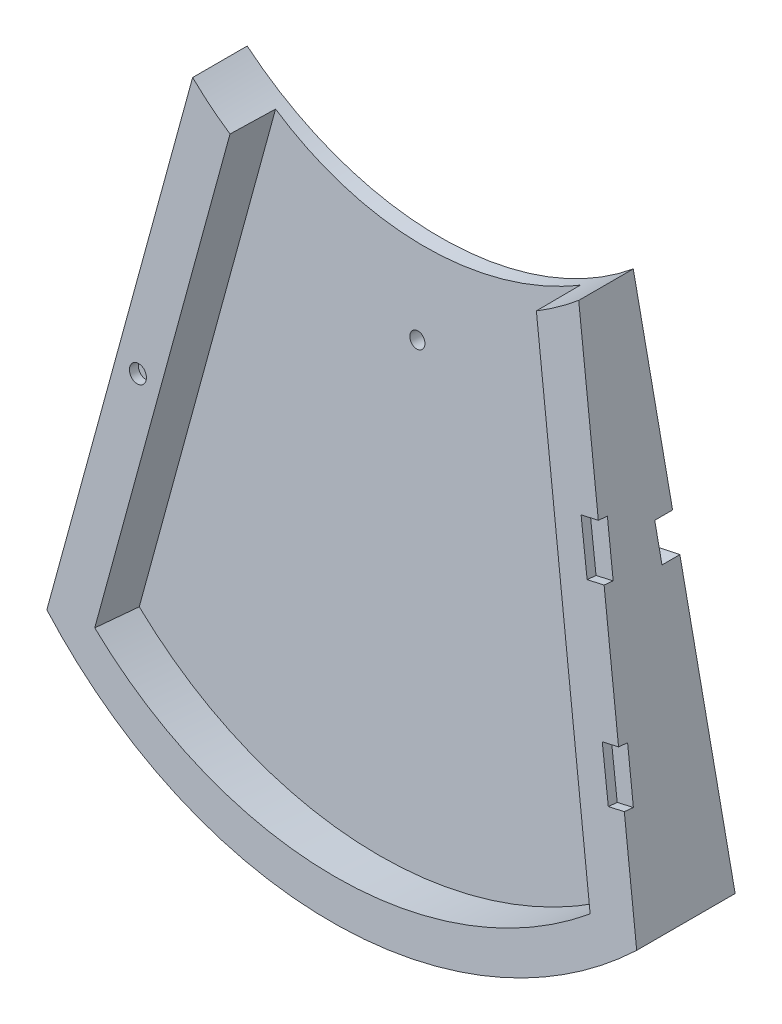
SolidWorks part; units mm, degrees
material "Oak"
ref_plane "Front Plane" through (0, 0, 0) normal (0, 0, 1) x (1, 0, 0)
ref_plane "Top Plane" through (0, 0, 0) normal (0, 1, 0) x (1, 0, 0)
ref_plane "Right Plane" through (0, 0, 0) normal (1, 0, 0) x (0, 0, -1)
sketch "Sketch2" plane through (0, 0, 0) normal (1, 0, 0) x (0, 0, -1)
  line L0 (-19.05, 177.8) -> (-34.9178, 0.7095)
  line L1 (-19.05, 177.8) -> (0, 177.8)
  line L4 (0, 177.8) -> (0, 0)
  line L5 (-34.9178, 0.7095) -> (-40.0182, -56.2125)
  line L6 (-40.0182, -56.2125) -> (0, -53.7905)
  line L7 (0, -53.7905) -> (0, 0)
  dimension "D1" = 19.05
  dimension "D2" = 34.925
  dimension "D3" = 177.8
  dimension "D4" = 57.15
extrude "Boss-Extrude1" add sketch "Sketch2" along normal blind 209.55
sketch "Sketch1" plane through (0, 0, 0) normal (0, 0, 1) x (1, 0, 0)
  line L0 (0, 0) -> (36.195, 174.0769)
  line L1 (173.355, 174.0769) -> (209.55, 0)
  line L2 (0, 0) -> (209.55, 0) construction
  line L3 (104.775, 149.4935) -> (104.775, -41.8231) construction
  line L4 (209.55, 177.8) -> (209.55, -56.2125) construction
  line L5 (-12.8433, 191.6723) -> (227.6672, 191.6723)
  line L6 (-12.8433, 191.6723) -> (-12.8433, -74.1551)
  line L7 (-12.8433, -74.1551) -> (227.6672, -74.1551)
  line L8 (227.6672, 191.6723) -> (227.6672, -74.1551)
  arc A2 (0, 0) -> (209.55, 0) centre (104.775, 110.6705) ccw
  arc A3 (36.195, 174.0769) -> (173.355, 174.0769) centre (104.775, 257.4435) ccw
  dimension "D1" = 107.95
  dimension "D3" = 152.4
  dimension "D2" = 177.8
  dimension "D4" = 137.16
  dimension "D5" = 215.9
extrude "Cut-Extrude1" cut sketch "Sketch1" along normal through all both and the other way through all
ref_plane "Plane1" through (0, -5.3911, -60.1672) normal (0, 0.0892, 0.996) x (1, 0, 0)
sketch "Sketch3" plane through (0, 3.4748, 34.67) normal (0, 0.0892, 0.996) x (1, 0, 0)
  line L0 (92.0294, 362.6105) -> (16.7736, -0.7763)
  line L1 (192.7764, -0.7763) -> (117.5206, 362.6105)
  line L2 (117.5206, 362.6105) -> (92.0294, 362.6105)
  line L3 (36.195, 171.2856) -> (0, -3.4887) construction
  line L4 (209.55, -3.4887) -> (173.355, 171.2856) construction
  arc A1 (16.7736, -0.7763) -> (192.7764, -0.7763) centre (104.775, 107.6252) ccw
  ellipse E0 centre (104.775, 107.6252) end of major axis (104.775, 260.6357) minor radius 152.4 (0, -3.4887) -> (209.55, -3.4887) ccw construction
  ellipse E1 centre (104.775, 254.9862) end of major axis (104.775, 363.3686) minor radius 107.95 (36.195, 171.2856) -> (173.355, 171.2856) ccw construction
  dimension "D2" = 15.875
extrude "Cut-Extrude2" cut sketch "Sketch3" against normal blind 15.875 contours L0 A1 L1 L2
sketch "Sketch4" plane through (0, 3.1095, 34.7027) normal (0, 0.0892, 0.996) x (1, 0, 0)
  line L0 (185.9702, 112.6051) -> (179.5857, 111.2457)
  line L2 (179.5857, 111.2457) -> (183.2886, 93.8555)
  line L3 (183.2886, 93.8555) -> (189.6731, 95.215)
  line L4 (189.6731, 95.215) -> (185.9702, 112.6051)
  line L5 (198.7566, 51.7026) -> (192.5459, 50.3802)
  line L6 (192.5459, 50.3802) -> (196.2488, 32.99)
  line L7 (196.2488, 32.99) -> (202.4595, 34.3125)
  line L8 (202.4595, 34.3125) -> (198.7566, 51.7026)
  line L9 (173.355, 173.3823) -> (209.55, 0) construction
  dimension "D1" = 17.78
  dimension "D2" = 38.1
  dimension "D3" = 44.45
  dimension "D4" = 6.35
extrude "Cut-Extrude3" cut sketch "Sketch4" against normal blind 3.175
sketch "Sketch5" plane through (0, 3.1095, 34.7027) normal (0, 0.0892, 0.996) x (1, 0, 0)
  line L0 (43.2755, 166.701) -> (6.8386, -9.2415) construction
  line L1 (36.195, 171.6524) -> (50.3561, 161.7497) construction
  line L2 (36.195, 171.6524) -> (0, -3.1219) construction
  circle A0 centre (25.0571, 78.7298) radius 3
  ellipse E1 centre (104.775, 107.992) end of major axis (104.775, 261.0025) minor radius 152.4 (0, -3.1219) -> (209.55, -3.1219) ccw construction
  dimension "D1" = 6
extrude "Cut-Extrude4" cut sketch "Sketch5" against normal blind 3.175
sketch "Sketch6" plane through (0, 0, 0) normal (0, 0, -1) x (-1, 0, 0)
  line L0 (-203.2, -5.6836) -> (-203.2, 0.6664)
  line L1 (-6.35, 0.6664) -> (-6.35, -5.6836)
  arc A1 (-203.2, 0.6664) -> (-6.35, 0.6664) centre (-104.775, 110.6705) ccw
  arc A2 (-203.2, -5.6836) -> (-6.35, -5.6836) centre (-104.775, 48.2914) ccw
  arc A3 (-209.55, 0) -> (0, 0) centre (-104.775, 110.6705) ccw construction
  dimension "D1" = 6.35
  dimension "D2" = 6.35
extrude "Cut-Extrude7" cut sketch "Sketch6" against normal blind 6.35 and the other way blind 3.175 contours A1 L1 A2 L0
sketch "Sketch7" plane through (0, 1.6927, 18.8911) normal (0, 0.0892, 0.996) x (1, 0, 0)
  circle A0 centre (104.775, 120.767) radius 2.667
  arc A2 (16.7736, -0.4095) -> (192.7764, -0.4095) centre (104.775, 107.992) ccw construction
  point P7 (104.775, -31.633)
  dimension "D1" = 5.334
  dimension "D2" = 152.4
extrude "Cut-Extrude8" cut sketch "Sketch7" against normal through all contours A0
sketch "Sketch8" plane through (0, 0, 0) normal (0, 0, -1) x (-1, 0, 0)
  line L0 (-187.325, 106.8893) -> (-189.9104, 94.4553)
  line L1 (-209.55, 0) -> (-173.355, 174.0769) construction
  line L2 (-189.9104, 94.4553) -> (-179.3414, 92.2577)
  line L3 (-179.3414, 92.2577) -> (-176.756, 104.6918)
  line L4 (-176.756, 104.6918) -> (-187.325, 106.8893)
  line L5 (-104.775, 121.9778) -> (-104.775, -41.7295) construction
  line L6 (-32.794, 104.6918) -> (-22.225, 106.8893)
  line L7 (-30.2086, 92.2577) -> (-32.794, 104.6918)
  line L8 (-19.6396, 94.4553) -> (-30.2086, 92.2577)
  line L9 (-22.225, 106.8893) -> (-19.6396, 94.4553)
  arc A0 (-203.2, -5.6836) -> (-6.35, -5.6836) centre (-104.775, 110.6705) ccw construction
  dimension "D1" = 12.7
  dimension "D2" = 10.795
  dimension "D3" = 82.55
extrude "Cut-Extrude9" cut sketch "Sketch8" against normal blind 6.35
